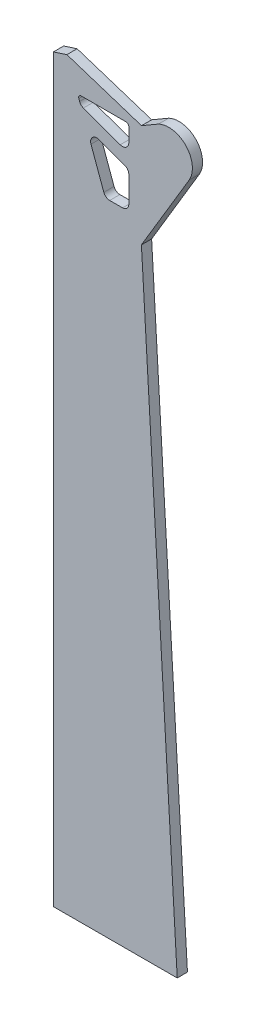
SolidWorks part; units mm, degrees
ref_plane "Front Plane" through (0, 0, 0) normal (0, 0, 1) x (1, 0, 0)
ref_plane "Top Plane" through (0, 0, 0) normal (0, 1, 0) x (1, 0, 0)
ref_plane "Right Plane" through (0, 0, 0) normal (1, 0, 0) x (0, 0, -1)
ref_plane "Plane1" through (0, 0, 3.875) normal (0, 0, 1) x (1, 0, 0)
sketch "Sketch1" plane through (0, 0, 3.875) normal (0, 0, 1) x (1, 0, 0)
  line L0 (8.9, -5.1) -> (8.8709, -5.1)
  arc A0 (9.0299, -5.3101) -> (8.9, -5.1) centre (15.7695, -1) cw
  spline S0 degree 3 poles (8.8709, -5.1) (8.9239, -5.17) (8.9769, -5.2401) (9.0299, -5.3101) knots 0 0 0 0 1 1 1 1
sketch "Sketch20" plane through (0, 0, 0) normal (0, 0, 1) x (1, 0, 0)
  line L1 (-31.5045, -56.0584) -> (75.0021, -56.0584) construction
  line L2 (-25.8989, 8.7762) -> (-25.8989, -64.5199) construction
  line L6 (-6.6408, -18.6441) -> (-6.3371, -19.4787)
  line L7 (9.5949, -26.2278) -> (-4.8429, -20.9729)
  line L8 (12.95, -18.3021) -> (12.95, -23.8786)
  line L10 (11.95, -17.3021) -> (-5.7011, -17.3021)
  line L11 (146.711, 52.1236) -> (-198.7383, 52.1236) construction
  line L20 (-1.8643, -31.7674) -> (3.1659, -45.5879)
  line L21 (5.4682, -47.2) -> (10.5, -47.2)
  line L22 (12.95, -34.5918) -> (12.95, -44.75)
  line L23 (1.2759, -28.6272) -> (11.3379, -32.2895)
  line L24 (-11.3097, -6.0698) -> (-16.5921, -7.7844) construction
  line L25 (-16.5921, -7.7844) -> (18.0707, -102.5712) construction
  line L28 (17.9385, -15.5715) -> (18.3682, -297.9996) construction
  line L29 (-16.5921, -7.7844) -> (-1.2832, -49.6473) construction
  line L30 (173.7942, -35.0525) -> (76.3124, -35.0525) construction
  line L31 (173.8678, -36.8) -> (76.3859, -36.8) construction
  line L32 (173.8678, -73.8) -> (76.3859, -73.8) construction
  line L33 (173.8678, -96.8) -> (18, -96.8) construction
  line L34 (173.8678, -100.8) -> (18, -100.8) construction
  line L37 (173.8678, -114) -> (88.8657, -114) construction
  line L39 (173.8678, -118) -> (88.8657, -118) construction
  line L41 (174.6, -35) -> (174.6, -298) construction
  line L42 (46.0249, -8.9573) -> (17.9029, -56.0584) construction
  line L44 (17.9029, -56.0584) -> (31.9512, -298) construction
  line L45 (31.9512, -298) -> (-16.5921, -298.0525) construction
  line L46 (-16.5921, -298.0525) -> (-16.5921, -7.7844) construction
  line L47 (-16.5921, -7.7844) -> (-11.3097, -6.0698) construction
  line L49 (17.9385, -15.5715) -> (29.2649, -8.9828) construction
  line L50 (29.2649, -8.9828) -> (46.0249, -8.9573) construction
  line L51 (36.6248, -24.7014) -> (17.9029, -56.0584)
  line L52 (17.9029, -56.0584) -> (31.9512, -298)
  line L53 (31.9512, -298) -> (-16.5921, -298.0525)
  line L54 (-16.5921, -298.0525) -> (-16.5921, -7.7844)
  line L55 (-16.5921, -7.7844) -> (-11.3097, -6.0698)
  line L56 (-11.3097, -6.0698) -> (17.9385, -15.5715)
  line L57 (17.9385, -15.5715) -> (24.5926, -11.7007)
  arc A0 (9.5949, -26.2278) -> (12.95, -23.8786) centre (10.45, -23.8786) ccw
  arc A2 (-6.3371, -19.4787) -> (-4.8429, -20.9729) centre (-3.9878, -18.6237) ccw
  arc A7 (5.4682, -47.2) -> (3.1659, -45.5879) centre (5.4682, -44.75) cw
  arc A8 (10.5, -47.2) -> (12.95, -44.75) centre (10.5, -44.75) ccw
  arc A9 (11.3379, -32.2895) -> (12.95, -34.5918) centre (10.5, -34.5918) cw
  arc A10 (-1.8643, -31.7674) -> (1.2759, -28.6272) centre (0.4379, -30.9295) cw
  arc A11 (36.6248, -24.7014) -> (24.5926, -11.7007) centre (28.6298, -20.0325) ccw
  arc A12 (12.95, -18.3021) -> (11.95, -17.3021) centre (11.95, -18.3021) ccw
  arc A13 (-6.6408, -18.6441) -> (-5.7011, -17.3021) centre (-5.7011, -18.3021) cw
  dimension "D2" = 1
  dimension "D4" = 145.837
  dimension "D7" = 1
  dimension "D10" = 9.2584
  dimension "D17" = 10.6845
  dimension "D9" = 6.6541
  dimension "D16" = 131.816
extrude "Boss-Extrude6" add sketch "Sketch20" along normal blind 4
